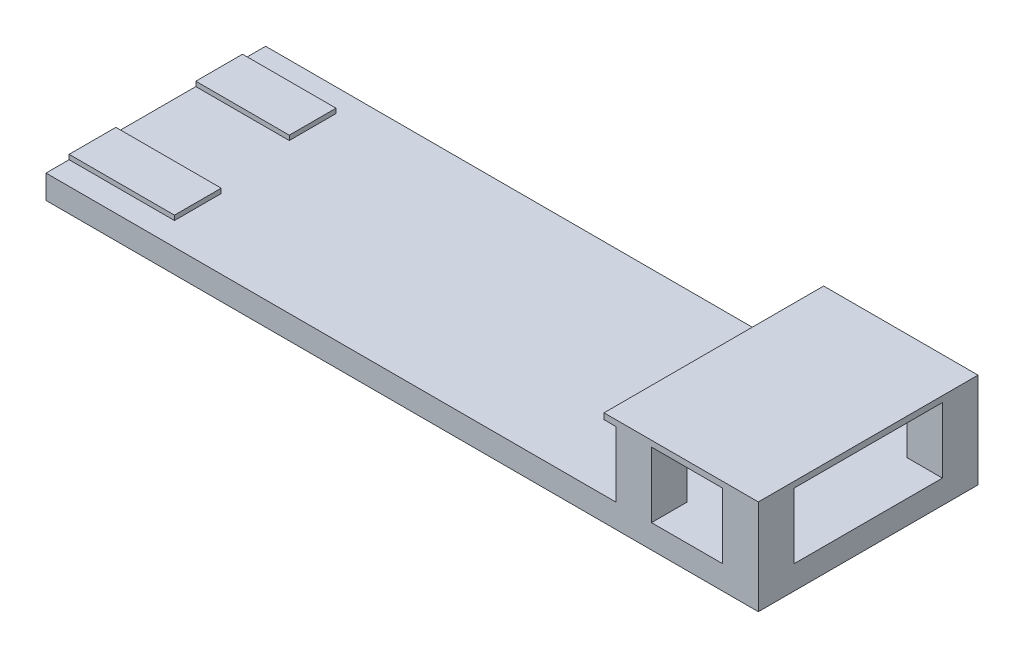
SolidWorks part; units mm, degrees
ref_plane "Front Plane" through (0, 0, 0) normal (0, 0, 1) x (1, 0, 0)
ref_plane "Top Plane" through (0, 0, 0) normal (0, 1, 0) x (1, 0, 0)
ref_plane "Right Plane" through (0, 0, 0) normal (1, 0, 0) x (0, 0, -1)
sketch "Sketch1" plane through (0, 0, 0) normal (0, 1, 0) x (1, 0, 0)
  line L0 (0, 0) -> (-188.1, 0) construction
  line L1 (-188.1, 117.475) -> (573.9, 117.475)
  line L2 (-188.1, 117.475) -> (-188.1, -117.475)
  line L3 (-188.1, -117.475) -> (573.9, -117.475)
  line L4 (573.9, 117.475) -> (573.9, -117.475)
  line L5 (-188.1, 42.75) -> (-188.1, 92.75) construction
  point P0 (0, 0)
  dimension "D1" = 234.95
  dimension "D2" = 762
extrude "Boss-Extrude1" add sketch "Sketch1" against normal mid plane 25.4
sketch "Sketch2" plane through (0, 12.7, 0) normal (0, 1, 0) x (1, 0, 0)
  line L0 (-188.1, -117.475) -> (573.9, -117.475) construction
  line L1 (573.9, 117.475) -> (535.8, 117.475)
  line L2 (573.9, 117.475) -> (573.9, 79.375)
  line L3 (573.9, 79.375) -> (535.8, 79.375)
  line L4 (535.8, 117.475) -> (535.8, 79.375)
  line L5 (573.9, -117.475) -> (535.8, -117.475)
  line L6 (573.9, -117.475) -> (573.9, -79.375)
  line L7 (573.9, -79.375) -> (535.8, -79.375)
  line L8 (535.8, -117.475) -> (535.8, -79.375)
  line L9 (421.5, -117.475) -> (459.6, -117.475)
  line L10 (421.5, -117.475) -> (421.5, -79.375)
  line L11 (421.5, -79.375) -> (459.6, -79.375)
  line L12 (459.6, -117.475) -> (459.6, -79.375)
  line L13 (573.9, 117.475) -> (-188.1, 117.475) construction
  line L14 (421.5, 117.475) -> (459.6, 117.475)
  line L15 (421.5, 117.475) -> (421.5, 79.375)
  line L16 (421.5, 79.375) -> (459.6, 79.375)
  line L17 (459.6, 117.475) -> (459.6, 79.375)
  dimension "D1" = 38.1
  dimension "D2" = 152.4
extrude "Boss-Extrude2" add sketch "Sketch2" along normal blind 70
sketch "Sketch3" plane through (0, 82.7, 0) normal (0, 1, 0) x (1, 0, 0)
  line L0 (-188.1, -117.475) -> (421.5, -117.475) construction
  line L1 (573.9, 117.475) -> (408.8, 117.475)
  line L2 (573.9, 117.475) -> (573.9, -117.475)
  line L3 (573.9, -117.475) -> (408.8, -117.475)
  line L4 (408.8, 117.475) -> (408.8, -117.475)
  dimension "D1" = 165.1
extrude "Boss-Extrude3" add sketch "Sketch3" along normal blind 6.35
sketch "Sketch4" plane through (0, 12.7, 0) normal (0, 1, 0) x (1, 0, 0)
  line L0 (-188.1, 117.475) -> (-188.1, -117.475) construction
  line L1 (-88.1, 42.75) -> (-188.1, 42.75)
  line L2 (-88.1, 42.75) -> (-88.1, 92.75)
  line L3 (-88.1, 92.75) -> (-188.1, 92.75)
  line L4 (-188.1, 42.75) -> (-188.1, 92.75)
  line L5 (-98.4688, 92.75) -> (-188.1, 92.75) construction
  line L6 (-85.7688, -42.75) -> (-175.4, -42.75) construction
  line L7 (-75.4, -92.75) -> (-188.1, -92.75)
  line L8 (-75.4, -92.75) -> (-75.4, -42.75)
  line L9 (-75.4, -42.75) -> (-188.1, -42.75)
  line L10 (-188.1, -92.75) -> (-188.1, -42.75)
extrude "Boss-Extrude4" add sketch "Sketch4" along normal blind 5
